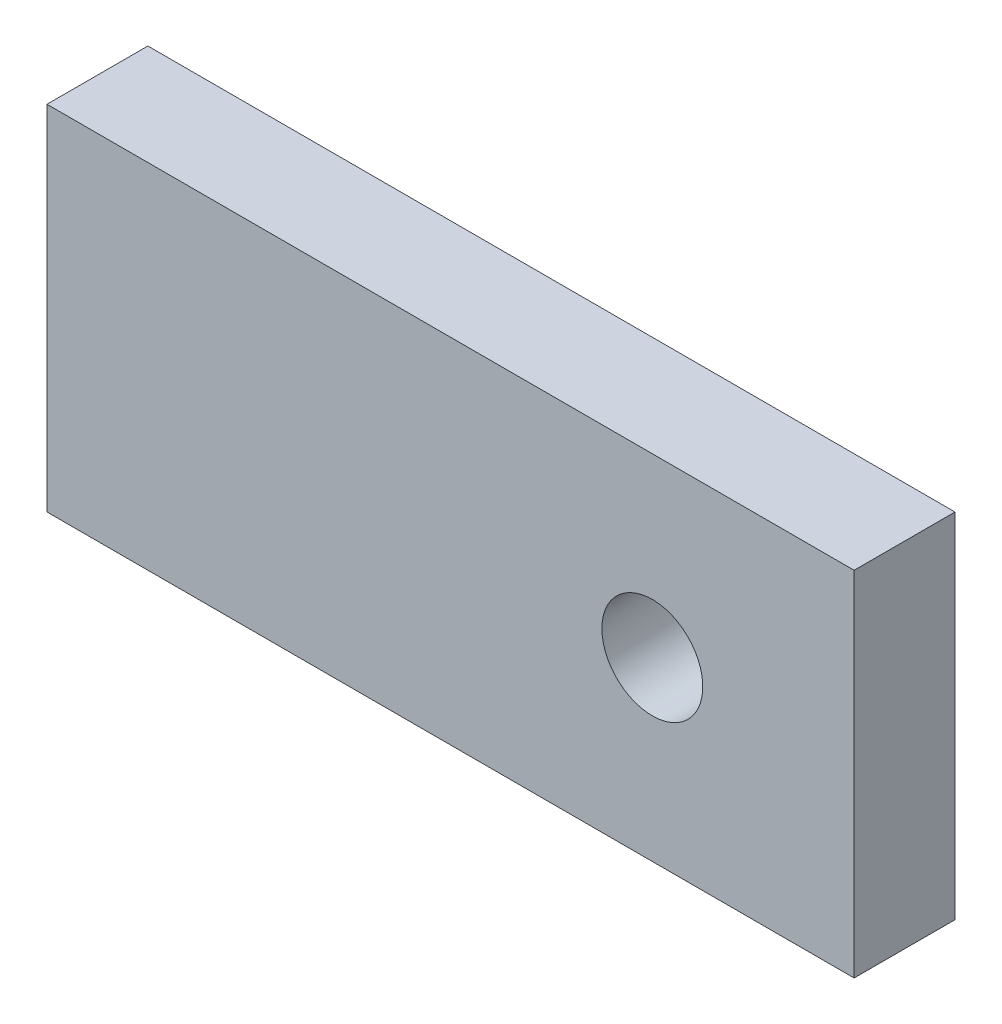
SolidWorks part; units mm, degrees
ref_plane "Front Plane" through (0, 0, 0) normal (0, 0, 1) x (1, 0, 0)
ref_plane "Top Plane" through (0, 0, 0) normal (0, 1, 0) x (1, 0, 0)
ref_plane "Right Plane" through (0, 0, 0) normal (1, 0, 0) x (0, 0, -1)
sketch "Sketch1" plane through (0, 0, 0) normal (0, 0, 1) x (1, 0, 0)
  line L1 (25.4, -11.1125) -> (-25.4, -11.1125)
  line L2 (25.4, -11.1125) -> (25.4, 11.1125)
  line L3 (25.4, 11.1125) -> (-25.4, 11.1125)
  line L4 (-25.4, -11.1125) -> (-25.4, 11.1125)
  line L5 (25.4, -11.1125) -> (-25.4, 11.1125) construction
  line L6 (25.4, 11.1125) -> (-25.4, -11.1125) construction
  circle A0 centre (12.7, 0) radius 2.5408
  point P0 (0, 0)
  dimension "D1" = 22.225
  dimension "D2" = 50.8
  dimension "D3" = 12.7
extrude "Boss-Extrude1" add sketch "Sketch1" along normal blind 6.35 contours A0 | L4 L1 L2 L3 A0
hole_wizard "1/4 (0.25) Diameter Hole1" positions "Sketch2" profile "Sketch3" hole size "1/4" standard "ANSI Inch" end condition through all
sketch "Sketch2" plane through (0, 0, 0) normal (0, 0, -1) x (-1, 0, 0)
  point P0 (-12.7, 0)
sketch "Sketch3" plane through (12.7, 0, 0) normal (1, 0, 0) x (0, 1, 0)
  line L0 (0, 0) -> (0, 6.35)
  line L1 (0, 6.35) -> (3.175, 6.35)
  line L2 (3.175, 6.35) -> (3.175, 0)
  line L5 (3.175, 0) -> (0, 0)
  line L11 (0, -6.35) -> (0, 107.95) construction
  dimension "Thru Hole Dia." = 6.35
  dimension "Thru Hole Depth" = 6.35
